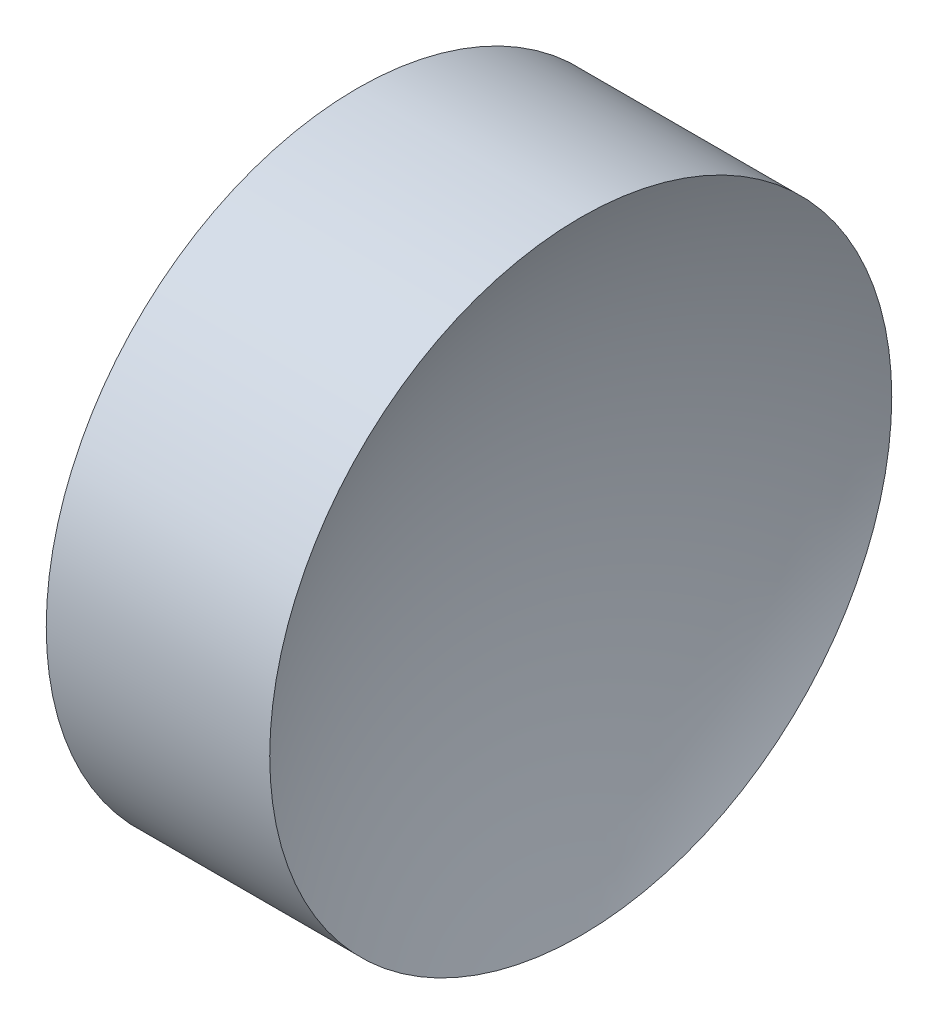
SolidWorks part; units mm, degrees
ref_plane "前视基准面" through (0, 0, 0) normal (0, 0, 1) x (1, 0, 0)
ref_plane "上视基准面" through (0, 0, 0) normal (0, 1, 0) x (1, 0, 0)
ref_plane "右视基准面" through (0, 0, 0) normal (1, 0, 0) x (0, 0, -1)
sketch "草图1" plane through (0, 0, 0) normal (0, 0, 1) x (1, 0, 0)
  line L0 (21.1565, 13.0311) -> (26.8361, 13.0311) construction
  line L1 (22.2009, 13.0311) -> (22.2009, 16.1811)
  line L2 (22.2009, 16.1811) -> (24.4644, 16.1811)
  line L3 (23.7009, 13.0311) -> (22.2009, 13.0311)
  arc A0 (24.4644, 16.1811) -> (23.7009, 13.0311) centre (30.5809, 13.0311) ccw
revolve "旋转1" add sketch "草图1" angle 360 about L0
